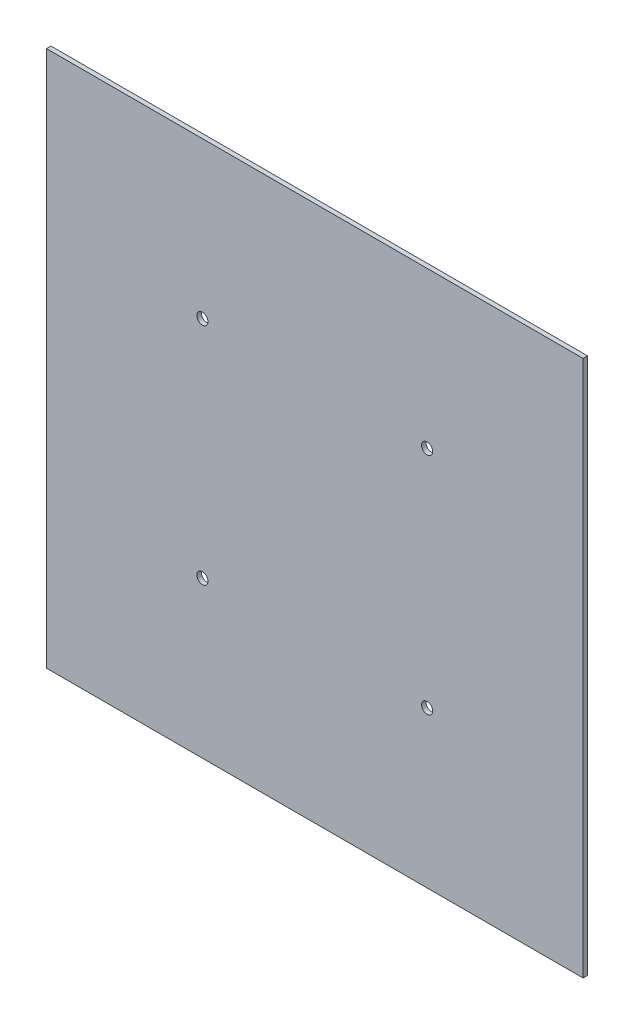
SolidWorks part; units mm, degrees
ref_plane "Front Plane" through (0, 0, 0) normal (0, 0, 1) x (1, 0, 0)
ref_plane "Top Plane" through (0, 0, 0) normal (0, 1, 0) x (1, 0, 0)
ref_plane "Right Plane" through (0, 0, 0) normal (1, 0, 0) x (0, 0, -1)
sketch "Sketch1" plane through (0, 0, 0) normal (0, 0, 1) x (1, 0, 0)
  line L0 (152.4, 304.8) -> (152.4, 0) construction
  line L1 (0, 0) -> (304.8, 0)
  line L2 (0, 0) -> (0, 304.8)
  line L3 (0, 304.8) -> (304.8, 304.8)
  line L4 (304.8, 0) -> (304.8, 304.8)
  line L5 (152.4, 0) -> (304.8, 152.4) construction
  line L6 (304.8, 152.4) -> (0, 152.4) construction
  line L7 (0, 152.4) -> (152.4, 304.8) construction
  circle A0 centre (88.575, 216.225) radius 3.175
  circle A1 centre (88.575, 88.575) radius 3.175
  circle A2 centre (216.225, 88.575) radius 3.175
  circle A3 centre (216.225, 216.225) radius 3.175
  dimension "D5" = 6.35
  dimension "D1" = 304.8
  dimension "D2" = 304.8
  dimension "D3" = 127.65
  dimension "D4" = 127.65
extrude "Boss-Extrude1" add sketch "Sketch1" along normal blind 2.54
